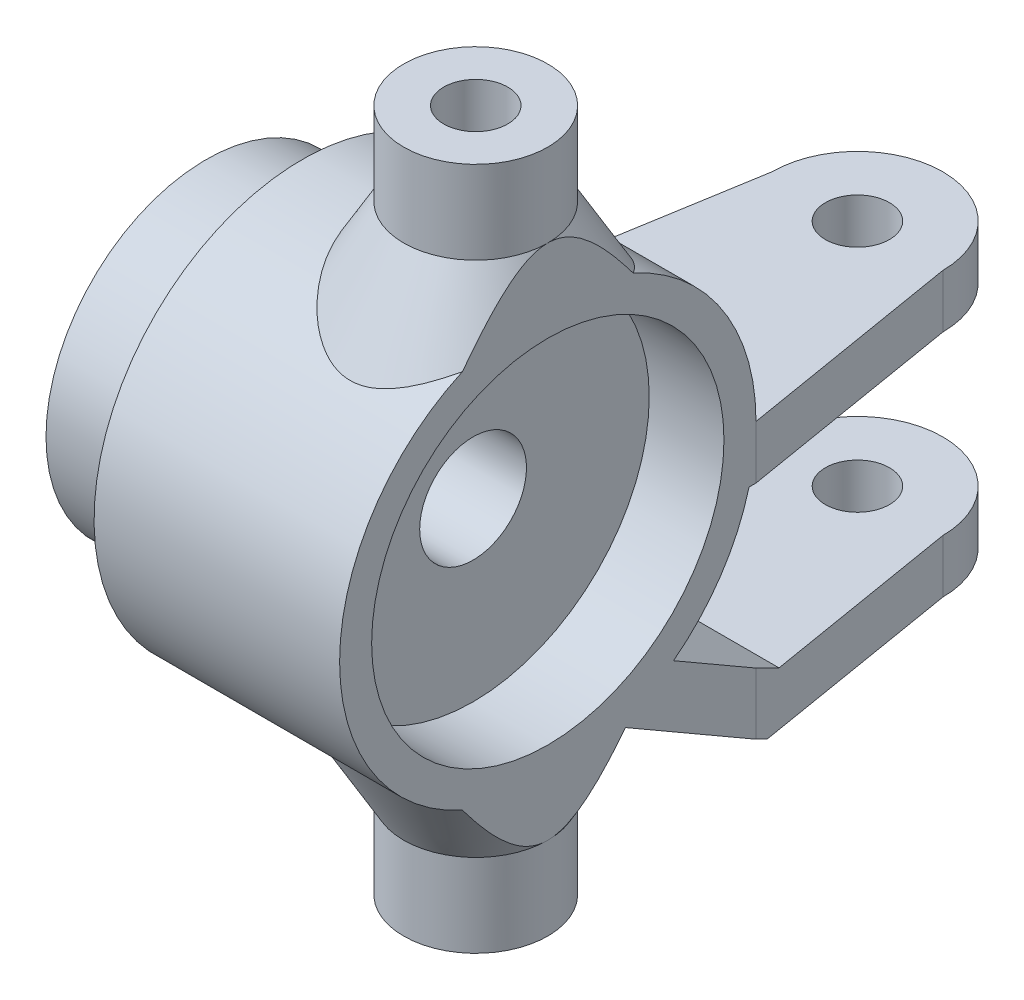
SolidWorks part; units mm, degrees
ref_plane "Front Plane" through (0, 0, 0) normal (0, 0, 1) x (1, 0, 0)
ref_plane "Top Plane" through (0, 0, 0) normal (0, 1, 0) x (1, 0, 0)
ref_plane "Right Plane" through (0, 0, 0) normal (1, 0, 0) x (0, 0, -1)
sketch "Sketch1" plane through (0, 0, 0) normal (0, 0, 1) x (1, 0, 0)
  line L0 (-29.0244, 0) -> (20.3659, 0) construction
  line L1 (-16, 2.5) -> (-16, 7.5)
  line L2 (-16, 7.5) -> (-12.5, 7.5)
  line L3 (-11.5, 8.5) -> (-11.5, 9.75)
  line L4 (-11.5, 9.75) -> (0, 9.75)
  line L5 (0, 9.75) -> (0, 8.25)
  line L6 (0, 8.25) -> (-3.5, 8.25)
  line L7 (-3.5, 8.25) -> (-3.5, 2.5)
  line L8 (-16, 2.5) -> (-3.5, 2.5)
  arc A0 (-12.5, 7.5) -> (-11.5, 8.5) centre (-12.5, 8.5) ccw
  point P5 (-16, 5)
  dimension "D8" = 1
  dimension "D1" = 5
  dimension "D2" = 15
  dimension "D3" = 19.5
  dimension "D4" = 1.5
  dimension "D5" = 4.5
  dimension "D6" = 12.5
  dimension "D7" = 16
revolve "Base Cylinder" add sketch "Sketch1" angle 360 about L0
ref_plane "Plane1" through (-3.375, 0, 0) normal (1, 0, 0) x (0, 0, -1)
sketch "Sketch2" plane through (-3.375, 0, 0) normal (1, 0, 0) x (0, 0, -1)
  line L0 (0, 16.8886) -> (0, -21.6127) construction
  line L1 (-3.375, 16) -> (-1.5, 16)
  line L2 (-1.5, 16) -> (-1.5, 9.6339)
  line L3 (-3.375, 16) -> (-3.375, 12.1113)
  line L4 (-3.375, 12.1113) -> (-5.875, 7.7812)
  circle A0 centre (0, 0) radius 9.75 construction
  arc A1 (-1.5, 9.6339) -> (-5.875, 7.7812) centre (0, 0) ccw
  point P12 (0, 9.75)
  dimension "D1" = 3
  dimension "D2" = 6.75
  dimension "D3" = 30
  dimension "D4" = 6.25
  dimension "D5" = 5
revolve "Suspension attachments" add sketch "Sketch2" angle 360 about L0
mirror "Mirror1" about plane through (0, 0, 0) normal (0, 1, 0) of "Suspension attachments"
sketch "Sketch3" plane through (0, 0, 0) normal (0, 0, 1) x (1, 0, 0)
  line L0 (0, 17.9363) -> (0, -18.3693)
  line L1 (0, -18.3693) -> (7.3027, -18.3693)
  line L2 (7.3027, -18.3693) -> (7.3027, 17.9363)
  line L3 (7.3027, 17.9363) -> (0, 17.9363)
extrude "Face Cut" cut sketch "Sketch3" against normal mid plane 20
sketch "Sketch5" plane through (0, 0, 0) normal (1, 0, 0) x (0, 0, -1)
  line L0 (9.75, 0) -> (20.25, 0)
  line L1 (20.25, 0) -> (20.25, -2.5)
  line L2 (20.25, -2.5) -> (9.424, -2.5)
  line L3 (5.887, -7.7721) -> (11.0449, -10.75)
  line L4 (11.0449, -10.75) -> (20.25, -10.75)
  line L5 (20.25, -10.75) -> (20.25, -13.25)
  line L6 (20.25, -13.25) -> (10.375, -13.25)
  line L7 (10.375, -13.25) -> (3.3099, -9.171)
  line L8 (3.375, -16) -> (3.375, -12.1113) construction
  arc A0 (4.0005, -8.8915) -> (4.0005, 8.8915) centre (0, 0) ccw construction
  arc A2 (3.3099, -9.171) -> (5.887, -7.7721) centre (0, 0) ccw
  arc A3 (9.424, -2.5) -> (9.75, 0) centre (0, 0) ccw
  dimension "D1" = 10.5
  dimension "D2" = 2.5
  dimension "D3" = 2.5
  dimension "D4" = 8.25
  dimension "D5" = 2.5
  dimension "D6" = 150
  dimension "D7" = 7
extrude "Link Arms" add sketch "Sketch5" against normal up to surface (11.5 mm away) up to face at (-11.5, 0, 8.5)
sketch "Sketch6" plane through (0, 0, 0) normal (0, 1, 0) x (1, 0, 0)
  line L0 (-11.5, 20.25) -> (0, 20.25) construction
  circle A0 centre (-5.75, 20.25) radius 4
  dimension "D1" = 8
extrude "Rounded Links" add sketch "Sketch6" against normal up to surface (13.25 mm away) up to face at (-5.75, -13.25, -15.3125)
sketch "Sketch7" plane through (0, 0, 0) normal (0, 1, 0) x (1, 0, 0)
  line L0 (-9.75, 20.25) -> (-11.5, 9.75)
  line L1 (-1.75, 20.25) -> (0, 9.75)
  line L2 (0, 9.75) -> (0, 20.25)
  line L3 (0, 20.25) -> (-1.75, 20.25)
  line L4 (-11.5, 9.75) -> (-11.5, 20.25)
  line L5 (-11.5, 20.25) -> (-9.75, 20.25)
  circle A0 centre (-5.75, 20.25) radius 1.5
  arc A1 (-1.75, 20.25) -> (-9.75, 20.25) centre (-5.75, 20.25) ccw construction
  dimension "D1" = 3
extrude "Trim 1" cut sketch "Sketch7" against normal up to surface (13.25 mm away) up to face at (-5.75, -13.25, -17.625)
sketch "Sketch8" plane through (1.5811, 0, -0.2635) normal (0.9864, 0, -0.1644) x (-0.1644, 0, -0.9864)
  line L0 (16.9198, -2.5) -> (16.9198, -10.75)
  line L1 (16.9198, -2.5) -> (16.9198, -10.75) construction
  line L2 (20.2622, -10.75) -> (10.9301, -10.75) construction
  line L3 (16.9198, -10.75) -> (24.9198, -10.75)
  line L4 (24.9198, -13.25) -> (24.9198, 0) construction
  line L5 (24.9198, -10.75) -> (24.9198, -2.5)
  line L6 (24.9198, -2.5) -> (16.9198, -2.5)
extrude "Trim 2" cut sketch "Sketch8" against normal mid plane 30
